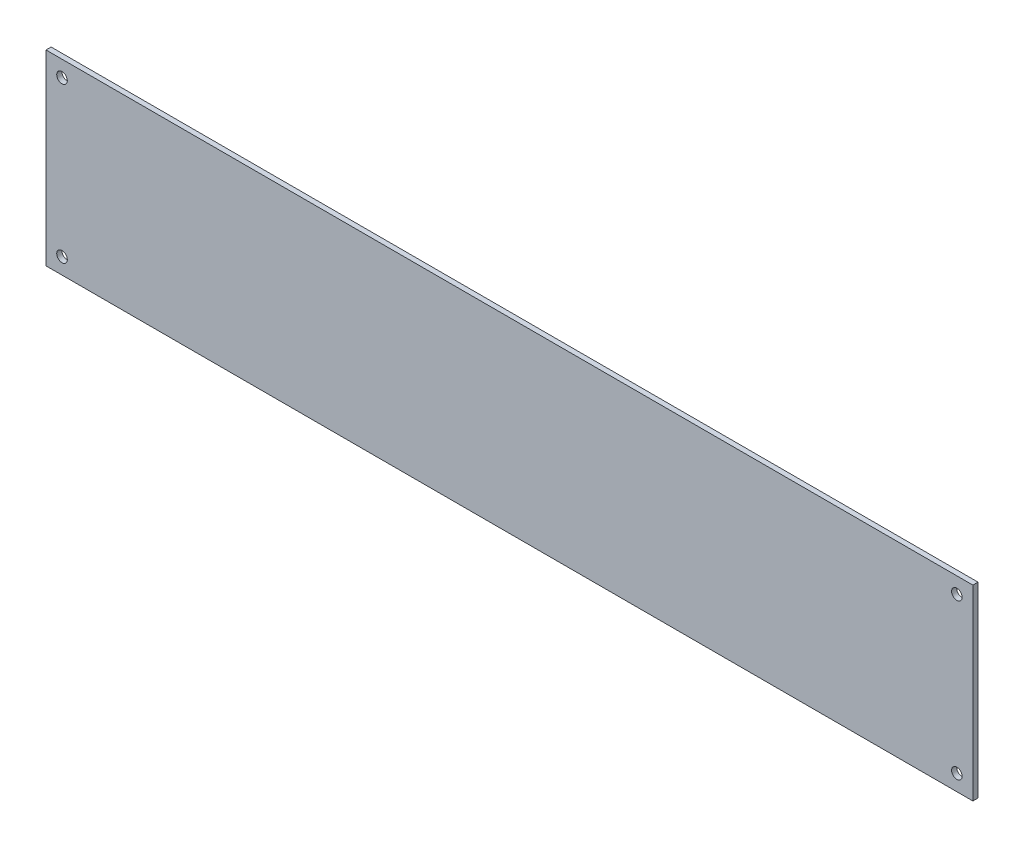
SolidWorks part; units mm, degrees
ref_plane "Płaszczyzna przednia" through (0, 0, 0) normal (0, 0, 1) x (1, 0, 0)
ref_plane "Płaszczyzna górna" through (0, 0, 0) normal (0, 1, 0) x (1, 0, 0)
ref_plane "Płaszczyzna prawa" through (0, 0, 0) normal (1, 0, 0) x (0, 0, -1)
sketch "Szkic1" plane through (0, 0, 0) normal (0, 0, 1) x (1, 0, 0)
  line L1 (0, 0) -> (289.561, 0)
  line L2 (0, 0) -> (0, 58.42)
  line L3 (0, 58.42) -> (289.561, 58.42)
  line L4 (289.561, 0) -> (289.561, 58.42)
  circle A0 centre (284.561, 5) radius 1.65
  circle A1 centre (284.561, 53.42) radius 1.65
  circle A2 centre (5, 53.42) radius 1.65
  circle A3 centre (5, 5) radius 1.65
  dimension "D3" = 3.3
  dimension "D12" = 3.3
  dimension "D13" = 3.3
  dimension "D14" = 3.3
  dimension "D1" = 58.42
  dimension "D2" = 289.561
  dimension "D4" = 5
  dimension "D5" = 5
  dimension "D6" = 5
  dimension "D7" = 5
  dimension "D8" = 5
  dimension "D9" = 5
  dimension "D10" = 5
  dimension "D11" = 5
extrude "Dodanie-wyciągnięcie1" add sketch "Szkic1" against normal blind 1.6
